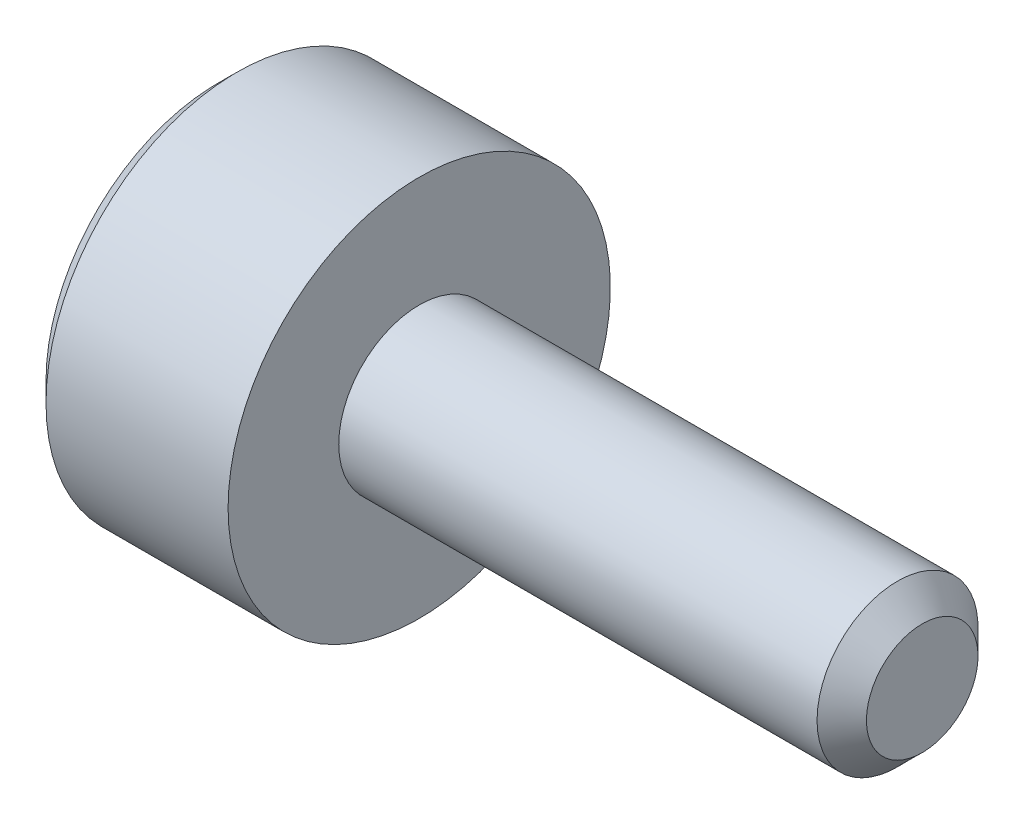
SolidWorks part; units mm, degrees
material "AISI 304"
ref_plane "正面" through (0, 0, 0) normal (0, 0, 1) x (1, 0, 0)
ref_plane "平面" through (0, 0, 0) normal (0, 1, 0) x (1, 0, 0)
ref_plane "右側面" through (0, 0, 0) normal (1, 0, 0) x (0, 0, -1)
ref_plane "Plane1" through (0, 0, 0) normal (0, 0, 1) x (1, 0, 0)
sketch "Sketch1" plane through (0, 0, 0) normal (0, 0, 1) x (1, 0, 0)
  line L0 (-2, 0) -> (-2, 1.71)
  line L1 (-2, 1.71) -> (-1.81, 1.9)
  line L2 (-1.81, 1.9) -> (0, 1.9)
  line L3 (0, 1.9) -> (0, 0.8)
  line L4 (0, 0.8) -> (4.7545, 0.8)
  line L5 (4.7545, 0.8) -> (5, 0.5545)
  line L6 (5, 0.5545) -> (5, 0)
  line L7 (5, 0) -> (-2, 0)
  line L8 (5, 0) -> (-2, 0) construction
  dimension "D1" = 0.8
revolve "Revolve1" add sketch "Sketch1" angle 360 about L8
cosmetic thread "Cosmetic Thread1" parameters "D1"=4.5748, "D2"=1.509
ref_plane "Plane2" through (-2, 0, 0) normal (1, 0, 0) x (0, 0, -1)
sketch "Sketch2" plane through (-2, 0, 0) normal (1, 0, 0) x (0, 0, -1)
  line L0 (-0.75, -0.433) -> (0, -0.866)
  line L1 (0, -0.866) -> (0.75, -0.433)
  line L2 (0.75, -0.433) -> (0.75, 0.433)
  line L3 (0.75, 0.433) -> (0, 0.866)
  line L4 (0, 0.866) -> (-0.75, 0.433)
  line L5 (-0.75, 0.433) -> (-0.75, -0.433)
extrude "Cut-Extrude1" cut sketch "Sketch2" along normal blind 0.8
